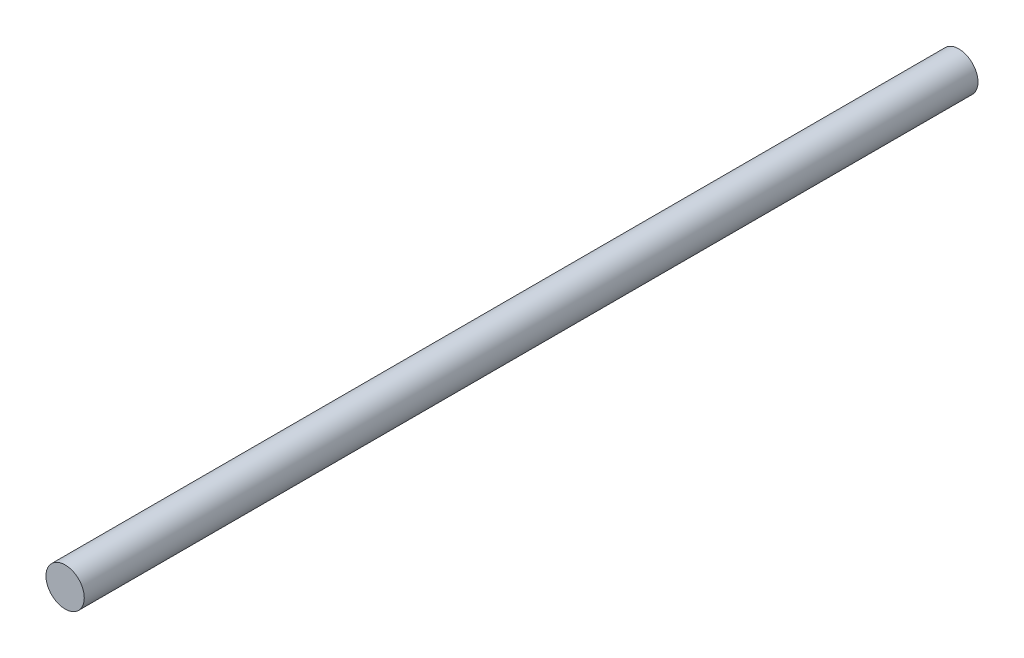
SolidWorks part; units mm, degrees
ref_plane "Front Plane" through (0, 0, 0) normal (0, 0, 1) x (1, 0, 0)
ref_plane "Top Plane" through (0, 0, 0) normal (0, 1, 0) x (1, 0, 0)
ref_plane "Right Plane" through (0, 0, 0) normal (1, 0, 0) x (0, 0, -1)
sketch "Sketch1" plane through (0, 0, 0) normal (0, 0, 1) x (1, 0, 0)
  circle A0 centre (0, 0) radius 3
  dimension "D1" = 6
extrude "Boss-Extrude1" add sketch "Sketch1" along normal blind 140
